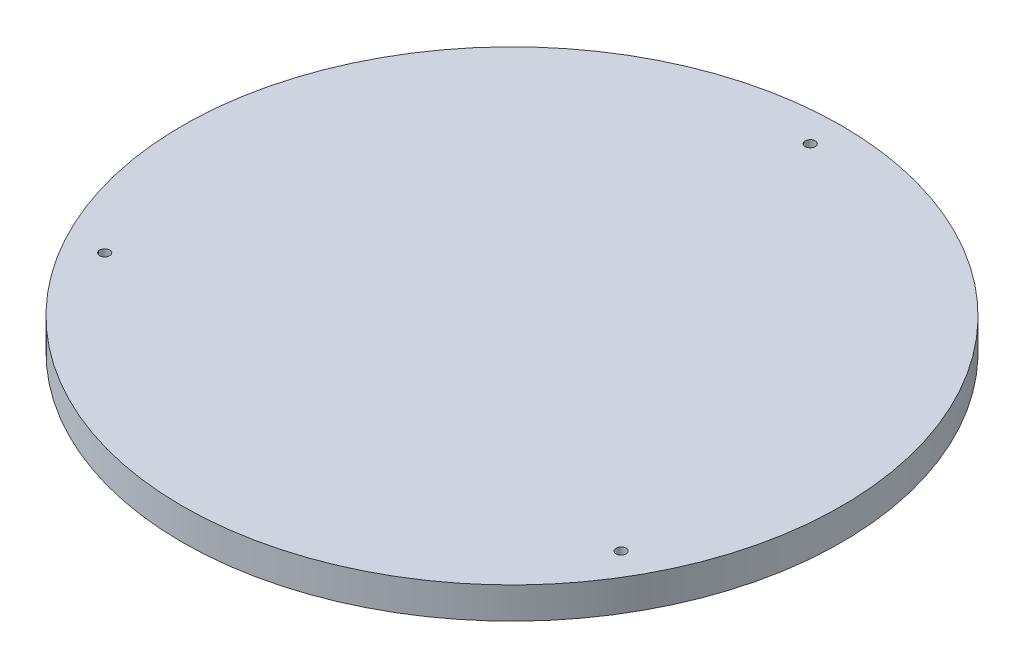
SolidWorks part; units mm, degrees
material "Glass"
ref_plane "Front Plane" through (0, 0, 0) normal (0, 0, 1) x (1, 0, 0)
ref_plane "Top Plane" through (0, 0, 0) normal (0, 1, 0) x (1, 0, 0)
ref_plane "Right Plane" through (0, 0, 0) normal (1, 0, 0) x (0, 0, -1)
sketch "Sketch1" plane through (0, 0, 0) normal (0, 1, 0) x (1, 0, 0)
  circle A0 centre (0, 0) radius 105
  dimension "D1" = 210
extrude "Boss-Extrude1" add sketch "Sketch1" along normal blind 10
sketch "Sketch2" plane through (0, 10, 0) normal (0, 1, 0) x (1, 0, 0)
  line L0 (0, 0) -> (0, 105) construction
  line L1 (0, 0) -> (-90.9327, -52.5) construction
  line L2 (0, 0) -> (90.9327, -52.5) construction
  circle A0 centre (0, 0) radius 105 construction
  circle A1 centre (-90.9327, -52.5) radius 15
  circle A2 centre (0, 105) radius 15
  circle A3 centre (90.9327, -52.5) radius 15
  dimension "D3" = 30
  dimension "D4" = 30
  dimension "D5" = 30
  dimension "D1" = 120
  dimension "D2" = 120
sketch "Sketch3" plane through (0, 10, 0) normal (0, 1, 0) x (1, 0, 0)
  line L0 (0, 0) -> (-90.9327, -52.5) construction
  line L1 (0, 0) -> (90.9327, -52.5) construction
  circle A0 centre (0, 0) radius 95
  circle A1 centre (-82.2724, -47.5) radius 1.6
  circle A2 centre (0, 95) radius 1.6
  circle A3 centre (82.2724, -47.5) radius 1.6
  dimension "D1" = 190
  dimension "D2" = 3.2
  dimension "D3" = 3.2
  dimension "D4" = 3.2
extrude "Cut-Extrude1" cut sketch "Sketch3" against normal blind 47 contours A0 A1 | A0 A1 | A0 A3 | A0 A3 | A0 A2 | A0 A2
